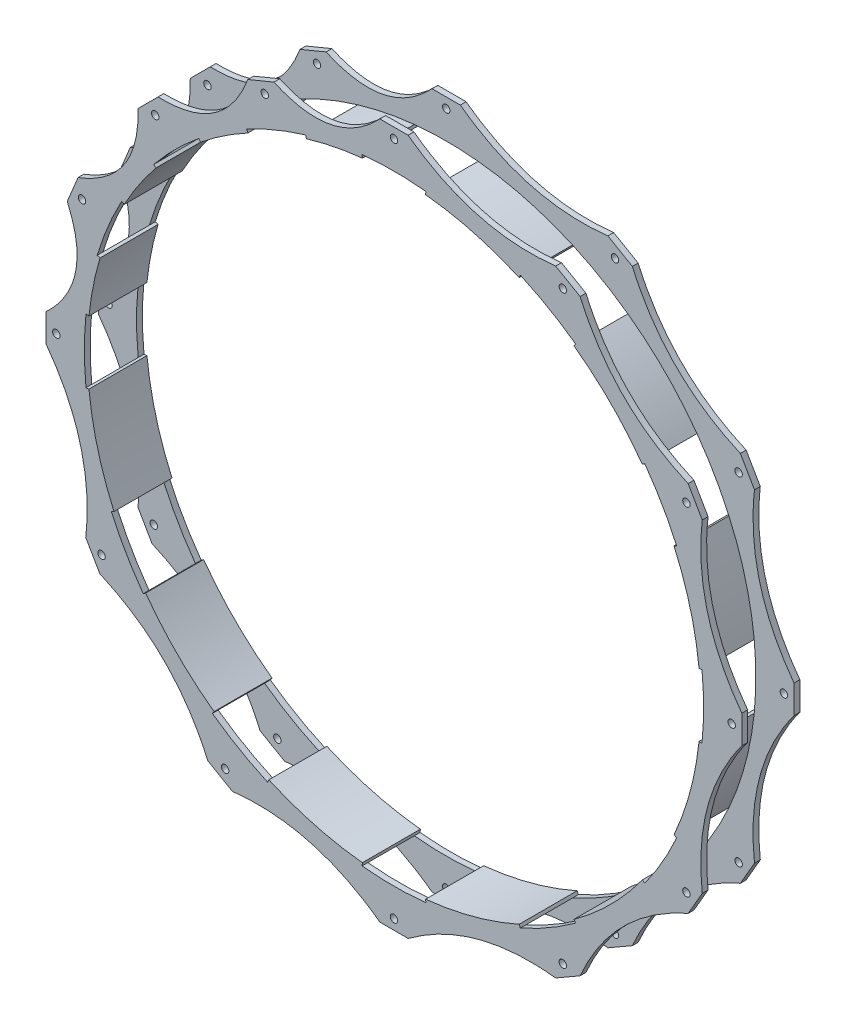
SolidWorks part; units mm, degrees
material "Maple"
ref_plane "Wasteboard" through (0, 0, 0) normal (0, 0, 1) x (1, 0, 0)
ref_plane "Left-Right" through (0, 0, 0) normal (0, 1, 0) x (1, 0, 0)
ref_plane "Front-Back" through (0, 0, 0) normal (1, 0, 0) x (0, 0, -1)
sketch "Sketch2" plane through (0, 0, 0) normal (0, 0, 1) x (1, 0, 0)
  line L0 (0, 0) -> (0, 50000) construction
  circle A0 centre (0, 0) radius 192.8812 construction
  circle A1 centre (0, 0) radius 209.55 construction
  circle A2 centre (0, 0) radius 172.72 construction
  circle A3 centre (0, 0) radius 252.73 construction
  circle A4 centre (0, 0) radius 184.785 construction
  circle A5 centre (0, 0) radius 190.5
  circle A6 centre (0, 0) radius 169.4688
  circle A7 centre (0, 0) radius 194.31 construction
  circle A8 centre (0, 184.785) radius 9.525 construction
  point P14 (0, 172.72)
  point P15 (0, 169.4688)
  point P16 (0, 175.26)
  dimension "D1" = 385.7625
  dimension "D2" = 419.1
  dimension "D3" = 2.54
  dimension "D4" = 505.46
  dimension "D5" = 369.57
  dimension "D6" = 381
  dimension "D7" = 3.2512
  dimension "D8" = 388.62
  dimension "D9" = 19.05
sketch "Sketch4" plane through (0, 0, 0) normal (0, 0, 1) x (1, 0, 0)
  line L0 (92.3925, 160.0285) -> (0, 184.785) construction
  line L1 (46.1963, 172.4068) -> (-12894.756, -48123.8846) construction
  line L2 (-7.7353, 190.3429) -> (7.7353, 190.3429)
  line L6 (-160.9741, -101.8704) -> (-168.7094, -88.4724)
  line L7 (-88.4724, -168.7094) -> (-101.8704, -160.9741)
  line L8 (7.7353, -190.3429) -> (-7.7353, -190.3429)
  line L9 (101.8704, -160.9741) -> (88.4724, -168.7094)
  line L10 (168.7094, -88.4724) -> (160.9741, -101.8704)
  line L11 (190.3429, 7.7353) -> (190.3429, -7.7353)
  line L12 (160.9741, 101.8704) -> (168.7094, 88.4724)
  line L13 (88.4724, 168.7094) -> (101.8704, 160.9741)
  line L14 (-101.8704, 160.9741) -> (-88.4724, 168.7094) [skipped]
  line L15 (-168.7094, 88.4724) -> (-160.9741, 101.8704) [skipped]
  line L16 (-79.9876, 172.8937) -> (-65.6945, 178.8141)
  line L17 (-70.7142, 170.7191) -> (0, 184.785) construction
  line L18 (-35.3571, 177.752) -> (9719.159, -48861.512) construction
  line L19 (-140.0625, 129.123) -> (-129.123, 140.0625)
  line L20 (-178.8141, 65.6945) -> (-172.8937, 79.9876)
  line L21 (-190.3429, -7.7353) -> (-190.3429, 7.7353)
  line L23 (-172.8937, -79.9876) -> (-178.8141, -65.6945) [skipped]
  line L24 (-190.3429, -7.7353) -> (-190.3429, 7.7353) [skipped]
  circle A0 centre (0, 184.785) radius 3.175 construction
  circle A1 centre (0, 184.785) radius 9.525 construction
  circle A2 centre (0, 184.785) radius 9.525 construction
  circle A3 centre (0, 0) radius 177.6413 construction
  circle A4 centre (0, 0) radius 190.5 construction
  circle A5 centre (0, 0) radius 184.785 construction
  circle A6 centre (0, 0) radius 169.4688 construction
  circle A7 centre (0, 0) radius 169.4688
  circle A8 centre (92.3925, 160.0285) radius 9.525 construction
  circle A9 centre (0, 0) radius 192.8812 construction
  circle A10 centre (0, 184.785) radius 2.032
  circle A14 centre (-160.0285, -92.3925) radius 2.032
  circle A15 centre (-92.3925, -160.0285) radius 2.032
  circle A16 centre (0, -184.785) radius 2.032
  circle A17 centre (92.3925, -160.0285) radius 2.032
  circle A18 centre (160.0285, -92.3925) radius 2.032
  circle A19 centre (184.785, 0) radius 2.032
  circle A20 centre (160.0285, 92.3925) radius 2.032
  circle A21 centre (92.3925, 160.0285) radius 2.032
  circle A22 centre (-160.0285, 92.3925) radius 2.032 [skipped]
  circle A23 centre (-92.3925, 160.0285) radius 2.032 [skipped]
  circle A24 centre (-70.7142, 170.7191) radius 9.525 construction
  circle A25 centre (-130.6627, 130.6627) radius 9.525 construction
  circle A26 centre (-170.7191, 70.7142) radius 9.525 construction
  circle A27 centre (-184.785, 0) radius 9.525 construction
  circle A28 centre (-70.7142, 170.7191) radius 2.032
  circle A29 centre (-130.6627, 130.6627) radius 2.032
  circle A30 centre (-170.7191, 70.7142) radius 2.032
  circle A31 centre (-184.785, 0) radius 2.032
  circle A32 centre (-184.785, 0) radius 2.032 [skipped]
  spline S0 degree 2 poles (7.7353, 190.3429) (43.85, 163.6504) (88.4724, 168.7094) knots 0 0 0 1 1 1
  spline S1 degree 2 poles (-65.6945, 178.8141) (-32.5972, 163.8774) (-7.7353, 190.3429) knots 0 0 0 1 1 1
  spline S2 degree 2 poles (-129.123, 140.0625) (-92.8291, 138.9285) (-79.9876, 172.8937) knots 0 0 0 1 1 1
  spline S3 degree 2 poles (-172.8937, 79.9876) (-138.9285, 92.8291) (-140.0625, 129.123) knots 0 0 0 1 1 1
  spline S4 degree 2 poles (-168.7094, -88.4724) (-163.6504, -43.85) (-190.3429, -7.7353) knots 0 0 0 1 1 1
  spline S5 degree 2 poles (-101.8704, -160.9741) (-119.8004, -119.8004) (-160.9741, -101.8704) knots 0 0 0 1 1 1
  spline S6 degree 2 poles (-7.7353, -190.3429) (-43.85, -163.6504) (-88.4724, -168.7094) knots 0 0 0 1 1 1
  spline S7 degree 2 poles (88.4724, -168.7094) (43.85, -163.6504) (7.7353, -190.3429) knots 0 0 0 1 1 1
  spline S8 degree 2 poles (160.9741, -101.8704) (119.8004, -119.8004) (101.8704, -160.9741) knots 0 0 0 1 1 1
  spline S9 degree 2 poles (190.3429, -7.7353) (163.6504, -43.85) (168.7094, -88.4724) knots 0 0 0 1 1 1
  spline S10 degree 2 poles (168.7094, 88.4724) (163.6504, 43.85) (190.3429, 7.7353) knots 0 0 0 1 1 1
  spline S11 degree 2 poles (101.8704, 160.9741) (119.8004, 119.8004) (160.9741, 101.8704) knots 0 0 0 1 1 1
  spline S12 degree 2 poles (-190.3429, 7.7353) (-163.8774, 32.5972) (-178.8141, 65.6945) knots 0 0 0 1 1 1
  point P6 (0, 0)
  point P18 (0, 0)
  point P19 (0, 0)
  point P21 (0, 0)
  point P24 (45.9769, 171.5883)
  point P29 (46.1963, 172.4068)
  point P31 (-7.7353, 190.3429)
  point P33 (-79.9876, 172.8937)
  point P34 (-65.6945, 178.8141)
  point P45 (0, 0)
  point P48 (-34.6561, 174.2279)
  point P103 (0, 0)
  point P112 (-35.3571, 177.752)
  point P123 (0, 0)
  point P126 (0, 0)
  dimension "D1" = 6.35
  dimension "D2" = 19.05
  dimension "D3" = 15.24
  dimension "D6" = 4.064
  dimension "D7" = 12
  dimension "D4" = 2
  dimension "D5" = 2
  dimension "D8" = 5
  dimension "D9" = 5
extrude "Boss-Extrude1" add sketch "Sketch4" along normal blind 3.175
ref_plane "Plane1" through (0, 0, 28.575) normal (0, 0, 1) x (1, 0, 0)
sketch "Sketch5" plane through (0, 0, 28.575) normal (0, 0, 1) x (1, 0, 0)
  line L13 (-129.123, 140.0625) -> (-140.0625, 129.123)
  line L14 (-65.6945, 178.8141) -> (-79.9876, 172.8937)
  line L15 (7.7353, 190.3429) -> (-7.7353, 190.3429)
  line L16 (101.8704, 160.9741) -> (88.4724, 168.7094)
  line L17 (168.7094, 88.4724) -> (160.9741, 101.8704)
  line L18 (190.3429, -7.7353) -> (190.3429, 7.7353)
  line L19 (160.9741, -101.8704) -> (168.7094, -88.4724)
  line L20 (88.4724, -168.7094) -> (101.8704, -160.9741)
  line L21 (-7.7353, -190.3429) -> (7.7353, -190.3429)
  line L22 (-101.8704, -160.9741) -> (-88.4724, -168.7094)
  line L23 (-168.7094, -88.4724) -> (-160.9741, -101.8704)
  line L24 (-190.3429, 7.7353) -> (-190.3429, -7.7353)
  line L25 (-172.8937, 79.9876) -> (-178.8141, 65.6945)
  line L26 (-129.123, 140.0625) -> (-140.0625, 129.123)
  line L27 (-65.6945, 178.8141) -> (-79.9876, 172.8937)
  line L28 (7.7353, 190.3429) -> (-7.7353, 190.3429)
  line L29 (101.8704, 160.9741) -> (88.4724, 168.7094)
  line L30 (168.7094, 88.4724) -> (160.9741, 101.8704)
  line L31 (190.3429, -7.7353) -> (190.3429, 7.7353)
  line L32 (160.9741, -101.8704) -> (168.7094, -88.4724)
  line L33 (88.4724, -168.7094) -> (101.8704, -160.9741)
  line L34 (-7.7353, -190.3429) -> (7.7353, -190.3429)
  line L35 (-101.8704, -160.9741) -> (-88.4724, -168.7094)
  line L36 (-168.7094, -88.4724) -> (-160.9741, -101.8704)
  line L37 (-190.3429, 7.7353) -> (-190.3429, -7.7353)
  line L38 (-172.8937, 79.9876) -> (-178.8141, 65.6945)
  circle A1 centre (0, 0) radius 169.4688
  circle A2 centre (0, 0) radius 169.4688
  circle A3 centre (0, 184.785) radius 2.032
  circle A4 centre (0, 184.785) radius 2.032
  circle A5 centre (-160.0285, -92.3925) radius 2.032
  circle A6 centre (-160.0285, -92.3925) radius 2.032
  circle A7 centre (-70.7142, 170.7191) radius 2.032
  circle A8 centre (-70.7142, 170.7191) radius 2.032
  circle A9 centre (92.3925, -160.0285) radius 2.032
  circle A10 centre (92.3925, -160.0285) radius 2.032
  circle A11 centre (0, -184.785) radius 2.032
  circle A12 centre (0, -184.785) radius 2.032
  circle A13 centre (-92.3925, -160.0285) radius 2.032
  circle A14 centre (-92.3925, -160.0285) radius 2.032
  circle A15 centre (184.785, 0) radius 2.032
  circle A16 centre (184.785, 0) radius 2.032
  circle A17 centre (160.0285, -92.3925) radius 2.032
  circle A18 centre (160.0285, -92.3925) radius 2.032
  circle A19 centre (92.3925, 160.0285) radius 2.032
  circle A20 centre (92.3925, 160.0285) radius 2.032
  circle A21 centre (160.0285, 92.3925) radius 2.032
  circle A22 centre (160.0285, 92.3925) radius 2.032
  circle A23 centre (-184.785, 0) radius 2.032
  circle A24 centre (-184.785, 0) radius 2.032
  circle A25 centre (-170.7191, 70.7142) radius 2.032
  circle A26 centre (-170.7191, 70.7142) radius 2.032
  circle A27 centre (-130.6627, 130.6627) radius 2.032
  circle A28 centre (-130.6627, 130.6627) radius 2.032
  parabola Q13 (-140.0625, 129.123) -> (-172.8937, 79.9876) focus (-164.8995, 110.1823) apex (-147.7033, 98.6922)
  parabola Q14 (-79.9876, 172.8937) -> (-129.123, 140.0625) focus (-110.1823, 164.8995) apex (-98.6922, 147.7033)
  parabola Q15 (-7.7353, 190.3429) -> (-65.6945, 178.8141) focus (-38.6909, 194.5123) apex (-34.6561, 174.2279)
  parabola Q16 (88.4724, 168.7094) -> (7.7353, 190.3429) focus (59.7292, 222.9123) apex (45.9769, 171.5883)
  parabola Q17 (160.9741, 101.8704) -> (101.8704, 160.9741) focus (163.1831, 163.1831) apex (125.6113, 125.6113)
  parabola Q18 (190.3429, 7.7353) -> (168.7094, 88.4724) focus (222.9123, 59.7292) apex (171.5883, 45.9769)
  parabola Q19 (168.7094, -88.4724) -> (190.3429, -7.7353) focus (222.9123, -59.7292) apex (171.5883, -45.9769)
  parabola Q20 (101.8704, -160.9741) -> (160.9741, -101.8704) focus (163.1831, -163.1831) apex (125.6113, -125.6113)
  parabola Q21 (7.7353, -190.3429) -> (88.4724, -168.7094) focus (59.7292, -222.9123) apex (45.9769, -171.5883)
  parabola Q22 (-88.4724, -168.7094) -> (-7.7353, -190.3429) focus (-59.7292, -222.9123) apex (-45.9769, -171.5883)
  parabola Q23 (-160.9741, -101.8704) -> (-101.8704, -160.9741) focus (-163.1831, -163.1831) apex (-125.6113, -125.6113)
  parabola Q24 (-190.3429, -7.7353) -> (-168.7094, -88.4724) focus (-222.9123, -59.7292) apex (-171.5883, -45.9769)
  parabola Q25 (-178.8141, 65.6945) -> (-190.3429, 7.7353) focus (-194.5123, 38.6909) apex (-174.2279, 34.6561)
  parabola Q26 (-140.0625, 129.123) -> (-172.8937, 79.9876) focus (-164.8995, 110.1823) apex (-147.7033, 98.6922)
  parabola Q27 (-79.9876, 172.8937) -> (-129.123, 140.0625) focus (-110.1823, 164.8995) apex (-98.6922, 147.7033)
  parabola Q28 (-7.7353, 190.3429) -> (-65.6945, 178.8141) focus (-38.6909, 194.5123) apex (-34.6561, 174.2279)
  parabola Q29 (88.4724, 168.7094) -> (7.7353, 190.3429) focus (59.7292, 222.9123) apex (45.9769, 171.5883)
  parabola Q30 (160.9741, 101.8704) -> (101.8704, 160.9741) focus (163.1831, 163.1831) apex (125.6113, 125.6113)
  parabola Q31 (190.3429, 7.7353) -> (168.7094, 88.4724) focus (222.9123, 59.7292) apex (171.5883, 45.9769)
  parabola Q32 (168.7094, -88.4724) -> (190.3429, -7.7353) focus (222.9123, -59.7292) apex (171.5883, -45.9769)
  parabola Q33 (101.8704, -160.9741) -> (160.9741, -101.8704) focus (163.1831, -163.1831) apex (125.6113, -125.6113)
  parabola Q34 (7.7353, -190.3429) -> (88.4724, -168.7094) focus (59.7292, -222.9123) apex (45.9769, -171.5883)
  parabola Q35 (-88.4724, -168.7094) -> (-7.7353, -190.3429) focus (-59.7292, -222.9123) apex (-45.9769, -171.5883)
  parabola Q36 (-160.9741, -101.8704) -> (-101.8704, -160.9741) focus (-163.1831, -163.1831) apex (-125.6113, -125.6113)
  parabola Q37 (-190.3429, -7.7353) -> (-168.7094, -88.4724) focus (-222.9123, -59.7292) apex (-171.5883, -45.9769)
  parabola Q38 (-178.8141, 65.6945) -> (-190.3429, 7.7353) focus (-194.5123, 38.6909) apex (-174.2279, 34.6561)
  dimension "D1" = 0
  dimension "D2" = 0
  dimension "D3" = 0
  dimension "D4" = 0
  dimension "D5" = 0
  dimension "D6" = 0
  dimension "D7" = 0
  dimension "D8" = 0
  dimension "D9" = 0
  dimension "D10" = 0
  dimension "D11" = 0
  dimension "D12" = 0
  dimension "D13" = 0
  dimension "D14" = 0
  dimension "D15" = 0
extrude "Boss-Extrude2" add sketch "Sketch5" along normal blind 3.175 separate body
sketch "Sketch6" plane through (0, 0, 31.75) normal (0, 0, 1) x (1, 0, 0)
  line L0 (0, 0) -> (5154.6392, 49733.5872) construction
  line L1 (0, 0) -> (20402.7451, 45647.8695) construction
  line L2 (17.471, 168.5658) -> (17.3034, 166.9489)
  line L3 (68.4892, 153.2337) -> (69.1526, 154.7178)
  line L4 (99.4133, 137.2468) -> (98.4596, 135.9303)
  line L5 (135.9303, 98.4596) -> (137.2468, 99.4133)
  line L6 (154.7178, 69.1526) -> (153.2337, 68.4892)
  line L7 (166.9489, 17.3034) -> (168.5658, 17.471)
  line L8 (168.5658, -17.471) -> (166.9489, -17.3034)
  line L9 (153.2337, -68.4892) -> (154.7178, -69.1526)
  line L10 (137.2468, -99.4133) -> (135.9303, -98.4596)
  line L11 (98.4596, -135.9303) -> (99.4133, -137.2468)
  line L12 (69.1526, -154.7178) -> (68.4892, -153.2337)
  line L39 (17.3034, -166.9489) -> (17.471, -168.5658)
  line L40 (-17.471, -168.5658) -> (-17.3034, -166.9489)
  line L41 (-68.4892, -153.2337) -> (-69.1526, -154.7178)
  line L42 (-99.4133, -137.2468) -> (-98.4596, -135.9303)
  line L43 (-135.9303, -98.4596) -> (-137.2468, -99.4133)
  line L44 (-154.7178, -69.1526) -> (-153.2337, -68.4892)
  line L45 (-166.9489, -17.3034) -> (-168.5658, -17.471)
  line L46 (0, 0) -> (68.4892, 153.2337) construction
  line L47 (0, 0) -> (135.9303, 98.4596) construction
  line L48 (0, 0) -> (-5154.6392, 49733.5872) construction
  line L49 (0, 0) -> (-14269.9542, 47920.4383) construction
  line L50 (-47.9023, 160.8624) -> (-48.3662, 162.4204)
  line L51 (-17.3034, 166.9489) -> (-17.471, 168.5658)
  line L52 (-105.8153, 130.2861) -> (-106.8402, 131.5479)
  line L53 (-79.8749, 147.6189) -> (-80.6485, 149.0487)
  line L54 (-147.6189, 79.8749) -> (-149.0487, 80.6485)
  line L55 (-130.2861, 105.8153) -> (-131.5479, 106.8402)
  line L56 (-166.9489, 17.3034) -> (-168.5658, 17.471)
  line L57 (-160.8624, 47.9023) -> (-162.4204, 48.3662)
  line L58 (0, 0) -> (-17.3034, 166.9489) construction
  line L59 (0, 0) -> (-79.8749, 147.6189) construction
  circle A0 centre (92.3925, 160.0285) radius 2.032 construction
  arc A1 (17.471, 168.5658) -> (69.1526, 154.7178) centre (0, 0) cw
  circle A2 centre (0, 0) radius 169.4688 construction
  arc A3 (17.3034, 166.9489) -> (68.4892, 153.2337) centre (0, 0) cw
  arc A4 (99.4133, 137.2468) -> (137.2468, 99.4133) centre (0, 0) cw
  arc A5 (98.4596, 135.9303) -> (135.9303, 98.4596) centre (0, 0) cw
  arc A6 (154.7178, 69.1526) -> (168.5658, 17.471) centre (0, 0) cw
  arc A7 (153.2337, 68.4892) -> (166.9489, 17.3034) centre (0, 0) cw
  arc A8 (168.5658, -17.471) -> (154.7178, -69.1526) centre (0, 0) cw
  arc A9 (166.9489, -17.3034) -> (153.2337, -68.4892) centre (0, 0) cw
  arc A10 (137.2468, -99.4133) -> (99.4133, -137.2468) centre (0, 0) cw
  arc A11 (135.9303, -98.4596) -> (98.4596, -135.9303) centre (0, 0) cw
  arc A12 (69.1526, -154.7178) -> (17.471, -168.5658) centre (0, 0) cw
  arc A13 (68.4892, -153.2337) -> (17.3034, -166.9489) centre (0, 0) cw
  arc A14 (-17.471, -168.5658) -> (-69.1526, -154.7178) centre (0, 0) cw
  arc A15 (-17.3034, -166.9489) -> (-68.4892, -153.2337) centre (0, 0) cw
  arc A16 (-99.4133, -137.2468) -> (-137.2468, -99.4133) centre (0, 0) cw
  arc A17 (-98.4596, -135.9303) -> (-135.9303, -98.4596) centre (0, 0) cw
  arc A18 (-154.7178, -69.1526) -> (-168.5658, -17.471) centre (0, 0) cw
  arc A19 (-153.2337, -68.4892) -> (-166.9489, -17.3034) centre (0, 0) cw
  circle A20 centre (-70.7142, 170.7191) radius 2.032 construction
  arc A21 (-48.3662, 162.4204) -> (-17.471, 168.5658) centre (0, 0) cw
  arc A22 (-47.9023, 160.8624) -> (-17.3034, 166.9489) centre (0, 0) cw
  arc A23 (-106.8402, 131.5479) -> (-80.6485, 149.0487) centre (0, 0) cw
  arc A24 (-105.8153, 130.2861) -> (-79.8749, 147.6189) centre (0, 0) cw
  arc A25 (-149.0487, 80.6485) -> (-131.5479, 106.8402) centre (0, 0) cw
  arc A26 (-147.6189, 79.8749) -> (-130.2861, 105.8153) centre (0, 0) cw
  arc A27 (-168.5658, 17.471) -> (-162.4204, 48.3662) centre (0, 0) cw
  arc A28 (-166.9489, 17.3034) -> (-160.8624, 47.9023) centre (0, 0) cw
  dimension "D3" = 19.05
  dimension "D7" = 19.05
  dimension "D2" = 19.05
  dimension "D4" = 1.6256
  dimension "D6" = 30
  dimension "D8" = 19.05
  dimension "D9" = 1.6256
  dimension "D11" = 22.5
  dimension "D5" = 9
  dimension "D10" = 4
extrude "Boss-Extrude3" add sketch "Sketch6" against normal through all
